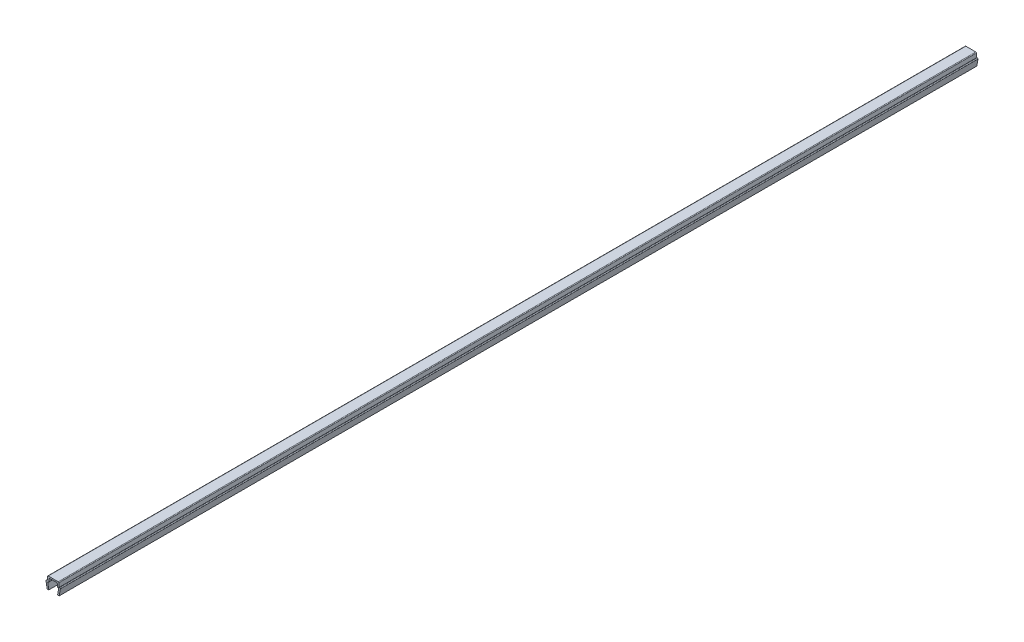
SolidWorks part; units mm, degrees
ref_plane "Front Plane" through (0, 0, 0) normal (0, 0, 1) x (1, 0, 0)
ref_plane "Top Plane" through (0, 0, 0) normal (0, 1, 0) x (1, 0, 0)
ref_plane "Right Plane" through (0, 0, 0) normal (1, 0, 0) x (0, 0, -1)
ref_plane "Plane1" through (0, 0, 0) normal (0, 0, 1) x (1, 0, 0)
sketch "Sketch1" plane through (0, 0, 0) normal (0, 0, 1) x (1, 0, 0)
  line L0 (-3.6, 3.35) -> (-3, 0)
  line L1 (-3, 0) -> (-2.2, 0)
  line L2 (-2.2, 0) -> (-2.7352, 2.9883)
  line L3 (-2.3907, 3.4) -> (-2.2, 3.4)
  line L4 (-2.2, 3.4) -> (-2.0705, 4.8805)
  line L5 (-1.7218, 5.2) -> (1.7218, 5.2)
  line L6 (2.0705, 4.8805) -> (2.2, 3.4)
  line L7 (2.2, 3.4) -> (2.3907, 3.4)
  line L8 (2.7352, 2.9883) -> (2.2, 0)
  line L9 (2.2, 0) -> (3, 0)
  line L10 (3, 0) -> (3.6, 3.35)
  line L11 (3.25, 3.7) -> (3, 3.7)
  line L12 (3, 3.7) -> (2.8355, 5.5805)
  line L13 (2.4868, 5.9) -> (-2.4868, 5.9)
  line L14 (-2.8355, 5.5805) -> (-3, 3.7)
  line L15 (-3, 3.7) -> (-3.25, 3.7)
  arc A0 (-2.7352, 2.9883) -> (-2.3907, 3.4) centre (-2.3907, 3.05) cw
  arc A1 (-2.0705, 4.8805) -> (-1.7218, 5.2) centre (-1.7218, 4.85) cw
  arc A2 (1.7218, 5.2) -> (2.0705, 4.8805) centre (1.7218, 4.85) cw
  arc A3 (2.3907, 3.4) -> (2.7352, 2.9883) centre (2.3907, 3.05) cw
  arc A4 (3.6, 3.35) -> (3.25, 3.7) centre (3.25, 3.35) ccw
  arc A5 (2.8355, 5.5805) -> (2.4868, 5.9) centre (2.4868, 5.55) ccw
  arc A6 (-2.4868, 5.9) -> (-2.8355, 5.5805) centre (-2.4868, 5.55) ccw
  arc A7 (-3.25, 3.7) -> (-3.6, 3.35) centre (-3.25, 3.35) ccw
extrude "Boss-Extrude1" add sketch "Sketch1" against normal mid plane 460
